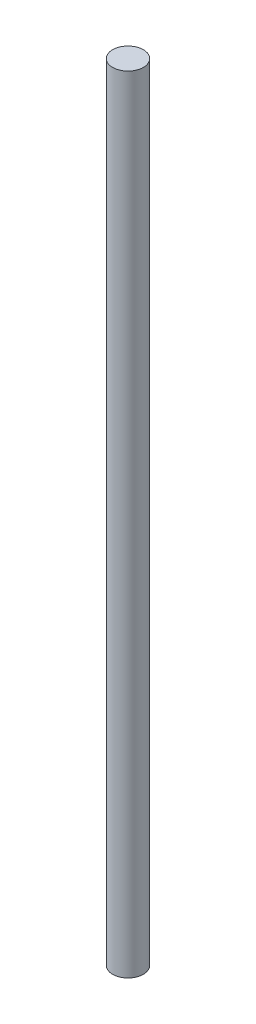
SolidWorks part; units mm, degrees
ref_plane "Front Plane" through (0, 0, 0) normal (0, 0, 1) x (1, 0, 0)
ref_plane "Top Plane" through (0, 0, 0) normal (0, 1, 0) x (1, 0, 0)
ref_plane "Right Plane" through (0, 0, 0) normal (1, 0, 0) x (0, 0, -1)
sketch "Sketch2" plane through (0, 0, 0) normal (0, 1, 0) x (1, 0, 0)
  circle A0 centre (-2.2578, 0.9951) radius 4.5
  dimension "D1" = 9
extrude "Boss-Extrude1" add sketch "Sketch2" against normal blind 230
